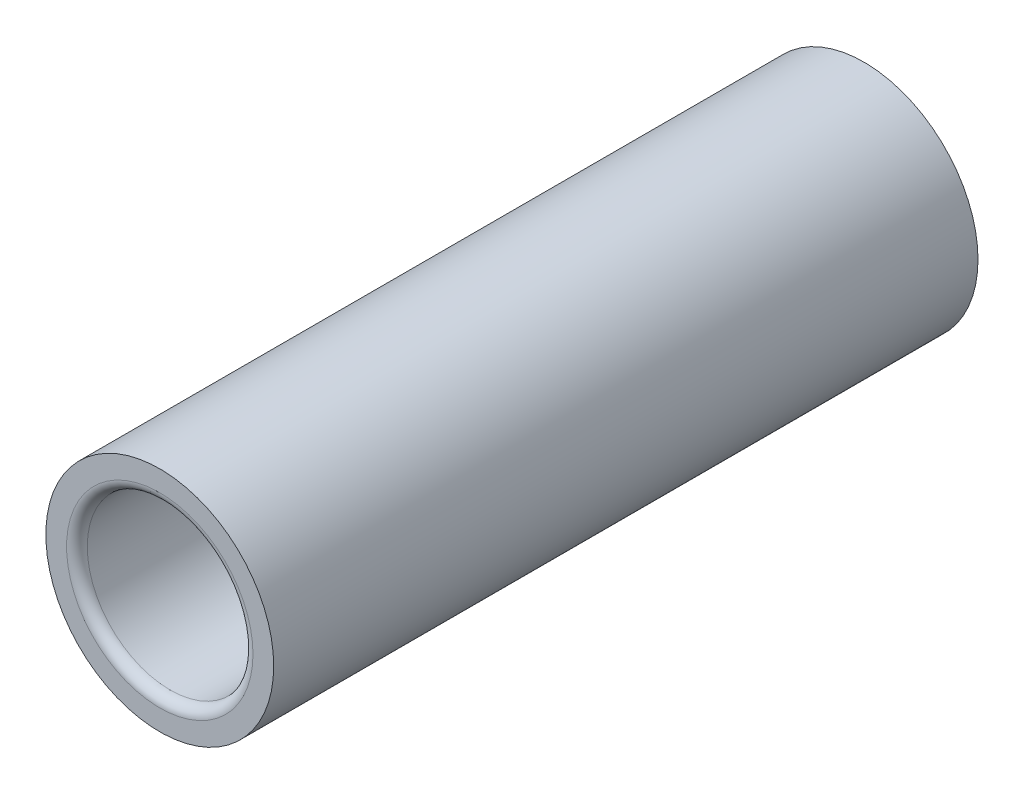
SolidWorks part; units mm, degrees
ref_plane "Front Plane" through (0, 0, 0) normal (0, 0, 1) x (1, 0, 0)
ref_plane "Top Plane" through (0, 0, 0) normal (0, 1, 0) x (1, 0, 0)
ref_plane "Right Plane" through (0, 0, 0) normal (1, 0, 0) x (0, 0, -1)
sketch "Sketch1" plane through (0, 0, 0) normal (0, 0, 1) x (1, 0, 0)
  circle A0 centre (0, 0) radius 8
  circle A1 centre (0, 0) radius 11
  dimension "D1" = 16
  dimension "D2" = 22
extrude "Boss-Extrude1" add sketch "Sketch1" along normal mid plane 68
fillet "Fillet1" radius 1 2 edges at (8, 0, -34) (8, 0, 34)
